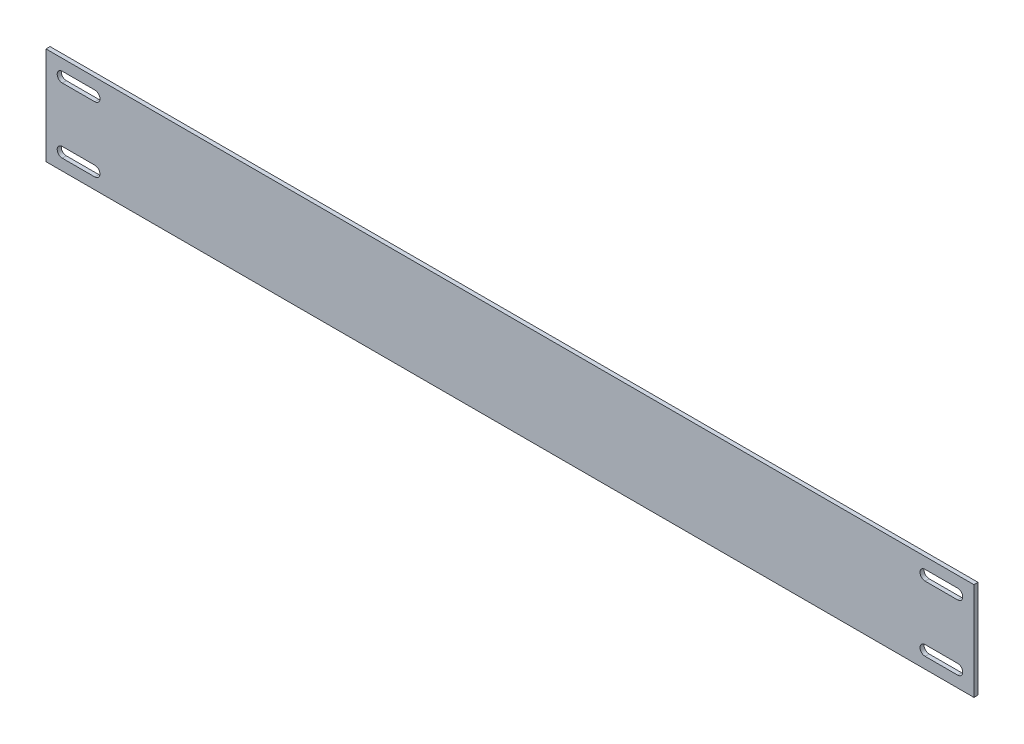
SolidWorks part; units mm, degrees
material "ABS PC"
ref_plane "Front Plane" through (0, 0, 0) normal (0, 0, 1) x (1, 0, 0)
ref_plane "Top Plane" through (0, 0, 0) normal (0, 1, 0) x (1, 0, 0)
ref_plane "Right Plane" through (0, 0, 0) normal (1, 0, 0) x (0, 0, -1)
sketch "Sketch1" plane through (0, 0, 0) normal (0, 1, 0) x (1, 0, 0)
  line L0 (0, 0) -> (361.95, 0)
  line L1 (361.95, 0) -> (361.95, 1.5875)
  line L2 (361.95, 1.5875) -> (336.55, 1.5875)
  line L5 (0, 0) -> (0, 1.5875)
  line L6 (0, 1.5875) -> (25.4, 1.5875)
  line L8 (25.4, 1.5875) -> (336.55, 1.5875)
  dimension "D1" = 361.95
  dimension "D2" = 25.4
  dimension "D3" = 1.5875
  dimension "D5" = 1.5875
  dimension "D6" = 25.4
extrude "Boss-Extrude1" add sketch "Sketch1" along normal blind 38.1
sketch "Sketch2" plane through (0, 0, -1.5875) normal (0, 0, -1) x (-1, 0, 0)
  line L0 (-180.975, 38.1) -> (-180.975, 0) construction
  line L3 (-25.4, 19.05) -> (0, 19.05) construction
  line L5 (0, 38.1) -> (0, 0) construction
  line L6 (-19.05, 31.75) -> (-6.35, 31.75) construction
  line L7 (-19.05, 33.7344) -> (-6.35, 33.7344)
  line L8 (-19.05, 29.7656) -> (-6.35, 29.7656)
  line L9 (-12.7, 19.05) -> (-12.7, 31.75) construction
  line L10 (-19.05, 6.35) -> (-6.35, 6.35) construction
  line L11 (-19.05, 4.3656) -> (-6.35, 4.3656)
  line L12 (-19.05, 8.3344) -> (-6.35, 8.3344)
  line L13 (-342.9, 6.35) -> (-355.6, 6.35) construction
  line L14 (-342.9, 4.3656) -> (-355.6, 4.3656)
  line L15 (-342.9, 8.3344) -> (-355.6, 8.3344)
  line L16 (-342.9, 31.75) -> (-355.6, 31.75) construction
  line L17 (-342.9, 33.7344) -> (-355.6, 33.7344)
  line L18 (-342.9, 29.7656) -> (-355.6, 29.7656)
  line L19 (0, 38.1) -> (0, 0) construction
  line L20 (-361.95, 38.1) -> (0, 38.1) construction
  line L21 (-361.95, 0) -> (0, 0) construction
  arc A0 (-19.05, 33.7344) -> (-19.05, 29.7656) centre (-19.05, 31.75) ccw
  arc A1 (-6.35, 29.7656) -> (-6.35, 33.7344) centre (-6.35, 31.75) ccw
  arc A2 (-19.05, 4.3656) -> (-19.05, 8.3344) centre (-19.05, 6.35) cw
  arc A3 (-6.35, 8.3344) -> (-6.35, 4.3656) centre (-6.35, 6.35) cw
  arc A4 (-342.9, 4.3656) -> (-342.9, 8.3344) centre (-342.9, 6.35) ccw
  arc A5 (-355.6, 8.3344) -> (-355.6, 4.3656) centre (-355.6, 6.35) ccw
  arc A6 (-342.9, 33.7344) -> (-342.9, 29.7656) centre (-342.9, 31.75) cw
  arc A7 (-355.6, 29.7656) -> (-355.6, 33.7344) centre (-355.6, 31.75) cw
  point P2 (-180.975, 38.1)
  point P14 (-12.7, 31.75)
  point P23 (-12.7, 6.35)
  point P30 (-349.25, 6.35)
  point P37 (-349.25, 31.75)
  dimension "D1" = 12.7
  dimension "D2" = 3.9688
  dimension "D3" = 12.7
  dimension "D4" = 12.7
extrude "Cut-Extrude2" cut sketch "Sketch2" against normal through all contours L8 A1 L7 A0 | A3 L12 A2 L11 | L15 A5 L14 A4 | A7 L18 A6 L17
